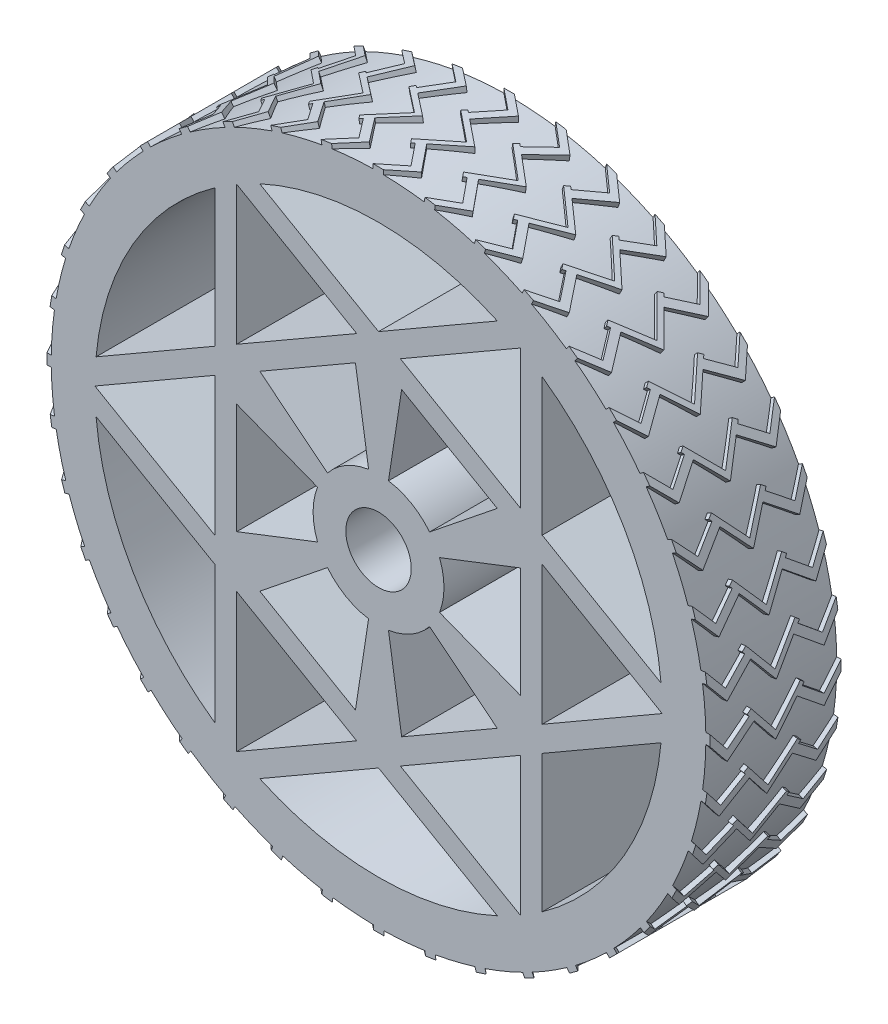
SolidWorks part; units mm, degrees
ref_plane "Alzado" through (0, 0, 0) normal (0, 0, 1) x (1, 0, 0)
ref_plane "Planta" through (0, 0, 0) normal (0, 1, 0) x (1, 0, 0)
ref_plane "Vista lateral" through (0, 0, 0) normal (1, 0, 0) x (0, 0, -1)
sketch "Croquis1" plane through (0, 0, 0) normal (0, 0, 1) x (1, 0, 0)
  line L0 (-32.5, -56.2917) -> (32.5, 56.2917) construction
  line L1 (64.7289, 5.93) -> (37.5, 21.6506)
  line L2 (-37.5, 53.0919) -> (-37.5, 21.6506)
  line L3 (-27.2289, -59.0219) -> (0, -43.3013)
  line L4 (-37.5, 15.8771) -> (-37.5, -15.8771)
  line L5 (27.2289, 59.0219) -> (0, 43.3013)
  line L6 (-64.7289, -5.93) -> (-37.5, -21.6506)
  line L7 (37.5, -53.0919) -> (37.5, -21.6506)
  line L8 (32.5, 56.2917) -> (5, 40.4145)
  line L9 (-65, 0) -> (-37.5, -15.8771)
  line L10 (32.5, -56.2917) -> (32.5, -24.5374)
  line L11 (65, 0) -> (37.5, 15.8771)
  line L12 (-32.5, 56.2917) -> (-32.5, 24.5374)
  line L13 (-32.5, -56.2917) -> (-5, -40.4145)
  line L14 (-32.5, 18.7639) -> (-32.5, -18.7639)
  line L15 (-37.5, 21.6506) -> (-64.7289, 5.93)
  line L16 (-37.5, 15.8771) -> (-65, 0)
  line L17 (-5, 40.4145) -> (-32.5, 24.5374)
  line L18 (0, 37.5278) -> (-32.5, 18.7639)
  line L19 (0, 43.3013) -> (-27.2289, 59.0219)
  line L20 (-5, 40.4145) -> (-32.5, 56.2917)
  line L21 (32.5, 24.5374) -> (5, 40.4145)
  line L22 (32.5, 18.7639) -> (0, 37.5278)
  line L23 (32.5, 24.5374) -> (32.5, 56.2917)
  line L24 (37.5, 21.6506) -> (37.5, 53.0919)
  line L25 (37.5, -15.8771) -> (65, 0)
  line L26 (37.5, -21.6506) -> (64.7289, -5.93)
  line L27 (37.5, -15.8771) -> (37.5, 15.8771)
  line L28 (32.5, -18.7639) -> (32.5, 18.7639)
  line L29 (5, -40.4145) -> (32.5, -24.5374)
  line L30 (0, -37.5278) -> (32.5, -18.7639)
  line L31 (0, -43.3013) -> (27.2289, -59.0219)
  line L32 (5, -40.4145) -> (32.5, -56.2917)
  line L33 (-32.5, -24.5374) -> (-32.5, -56.2917)
  line L34 (-37.5, -21.6506) -> (-37.5, -53.0919)
  line L35 (-32.5, -18.7639) -> (0, -37.5278)
  line L36 (-32.5, -24.5374) -> (-5, -40.4145)
  circle A0 centre (0, 0) radius 75
  arc A1 (-32.4519, 18.7917) -> (18.75, 32.476) centre (0, 0) ccw construction
  arc A2 (-32.4519, 18.7917) -> (18.75, 32.476) centre (0, 0) ccw construction
  arc A3 (-37.5, 53.0919) -> (-64.7289, 5.93) centre (0, 0) ccw
  circle A4 centre (0, 0) radius 32.5 construction
  circle A5 centre (0, 0) radius 32.5 construction
  arc A6 (0.0481, 37.5) -> (-18.75, 32.476) centre (0, 0) ccw construction
  arc A7 (0.0481, 37.5) -> (-18.75, 32.476) centre (0, 0) ccw construction
  arc A8 (-64.7289, -5.93) -> (-37.5, -53.0919) centre (0, 0) ccw
  arc A9 (-27.2289, -59.0219) -> (27.2289, -59.0219) centre (0, 0) ccw
  arc A10 (37.5, -53.0919) -> (64.7289, -5.93) centre (0, 0) ccw
  arc A11 (64.7289, 5.93) -> (37.5, 53.0919) centre (0, 0) ccw
  arc A12 (27.2289, 59.0219) -> (-27.2289, 59.0219) centre (0, 0) ccw
  dimension "D1" = 150
  dimension "D2" = 5
  dimension "D3" = 5
extrude "Saliente-Extruir1" add sketch "Croquis1" along normal mid plane 30
sketch "Croquis2" plane through (0, 0, 0) normal (0, 0, 1) x (1, 0, 0)
  circle A0 centre (0, 0) radius 15
  dimension "D1" = 30
extrude "Saliente-Extruir2" add sketch "Croquis2" along normal mid plane 30 separate body
sketch "Croquis3" plane through (0, 0, 0) normal (0, 0, 1) x (1, 0, 0)
  line L0 (0, 0) -> (27.2065, 21.8201)
  line L1 (32.5, 18.7639) -> (0, 37.5278) construction
  line L2 (0, 0) -> (32.5, 12.6515)
  line L3 (32.5, -18.7639) -> (32.5, 18.7639) construction
  line L4 (32.5, 12.6515) -> (32.5, 18.7639)
  line L5 (32.5, 18.7639) -> (27.2065, 21.8201)
  line L6 (32.5, -18.7639) -> (32.5, -12.6515)
  line L7 (0, 0) -> (32.5, -12.6515)
  line L8 (0, 0) -> (27.2065, -21.8201)
  line L9 (27.2065, -21.8201) -> (32.5, -18.7639)
  line L10 (0, -37.5278) -> (5.2935, -34.4716)
  line L11 (0, 0) -> (5.2935, -34.4716)
  line L12 (0, 0) -> (-5.2935, -34.4716)
  line L13 (-5.2935, -34.4716) -> (0, -37.5278)
  line L14 (-32.5, -18.7639) -> (-27.2065, -21.8201)
  line L15 (0, 0) -> (-27.2065, -21.8201)
  line L16 (0, 0) -> (-32.5, -12.6515)
  line L17 (-32.5, -12.6515) -> (-32.5, -18.7639)
  line L18 (-32.5, 18.7639) -> (-32.5, 12.6515)
  line L19 (0, 0) -> (-32.5, 12.6515)
  line L20 (0, 0) -> (-27.2065, 21.8201)
  line L21 (-27.2065, 21.8201) -> (-32.5, 18.7639)
  line L22 (0, 37.5278) -> (-5.2935, 34.4716)
  line L23 (0, 0) -> (-5.2935, 34.4716)
  line L24 (0, 0) -> (5.2935, 34.4716)
  line L25 (5.2935, 34.4716) -> (0, 37.5278)
  point P27 (0, 0)
  dimension "D1" = 6
extrude "Saliente-Extruir3" add sketch "Croquis3" along normal mid plane 30 contours L24 L25 L22 L23 | L20 L21 L18 L19 | L16 L17 L14 L15 | L12 L13 L10 L11 | L8 L9 L6 L7 | L4 L5 L0 L2
sketch "Croquis4" plane through (0, 0, -15) normal (0, 0, -1) x (-1, 0, 0)
  circle A0 centre (0, 0) radius 7.5
  dimension "D1" = 15
extrude "Cortar-Extruir1" cut sketch "Croquis4" against normal blind 30
ref_plane "Plano1" through (-75, 0, 0) normal (-1, 0, 0) x (0, 0, 1)
sketch "Croquis6" plane through (-75, 0, 0) normal (-1, 0, 0) x (0, 0, 1)
  line L0 (0, 5.1841) -> (-5.6413, -1.8033)
  line L1 (-5.6413, -1.8033) -> (-6.5573, -1.0638)
  line L2 (-6.5573, -1.0638) -> (-6.0993, -0.4966)
  line L3 (-6.0993, -0.4966) -> (-11.1041, 3.5441)
  line L4 (-11.1041, 3.5441) -> (-15, -1.2814)
  line L5 (-15, 75) -> (-15, -75) construction
  line L6 (-15, -1.2814) -> (-15, 1.1313)
  line L7 (-15, 1.1313) -> (-11.1041, 5.9569)
  line L8 (-11.1041, 5.9569) -> (-4.92, 0.9641)
  line L9 (-4.92, 0.9641) -> (0, 7.0581)
  line L10 (0, 0) -> (0, 5.1841) construction
  line L12 (0, 5.1841) -> (5.6413, -1.8033)
  line L13 (5.6413, -1.8033) -> (6.5573, -1.0638)
  line L14 (6.5573, -1.0638) -> (6.0993, -0.4966)
  line L15 (6.0993, -0.4966) -> (11.1041, 3.5441)
  line L16 (11.1041, 3.5441) -> (15, -1.2814)
  line L17 (15, -1.2814) -> (15, 1.1313)
  line L18 (15, 1.1313) -> (11.1041, 5.9569)
  line L19 (11.1041, 5.9569) -> (4.92, 0.9641)
  line L20 (4.92, 0.9641) -> (0, 7.0581)
extrude "Saliente-Extruir4" add sketch "Croquis6" along normal mid plane 2
pattern_circular "MatrizC1" count 40 over 360 about axis through (0, 0, 0) along (0, 0, 1) of "Saliente-Extruir4"
